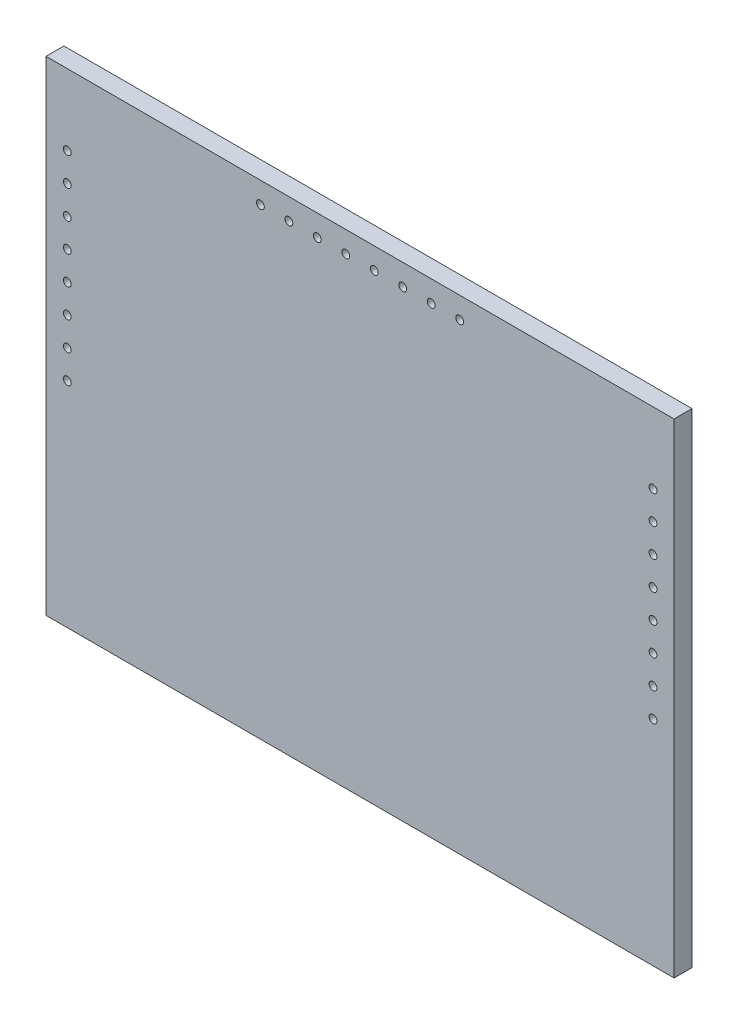
SolidWorks part; units mm, degrees
ref_plane "Plano frontal" through (0, 0, 0) normal (0, 0, 1) x (1, 0, 0)
ref_plane "Plano superior" through (0, 0, 0) normal (0, 1, 0) x (1, 0, 0)
ref_plane "Plano direito" through (0, 0, 0) normal (1, 0, 0) x (0, 0, -1)
sketch "Esboço1" plane through (0, 0, 0) normal (0, 0, 1) x (1, 0, 0)
  line L1 (-140.25, 108.115) -> (140.25, 108.115)
  line L2 (-140.25, 108.115) -> (-140.25, -108.115)
  line L3 (-140.25, -108.115) -> (140.25, -108.115)
  line L4 (140.25, 108.115) -> (140.25, -108.115)
  line L5 (-140.25, 108.115) -> (140.25, -108.115) construction
  line L6 (-140.25, -108.115) -> (140.25, 108.115) construction
  point P0 (0, 0)
  dimension "D1" = 280.5
  dimension "D2" = 216.23
extrude "Ressalto-extrusão1" add sketch "Esboço1" along normal blind 8
sketch "Esboço2" plane through (0, 0, 8) normal (0, 0, 1) x (1, 0, 0)
  line L2 (140.25, 108.115) -> (-140.25, 108.115) construction
  line L3 (140.25, -108.115) -> (140.25, 108.115) construction
  circle A0 centre (44.5, 98.615) radius 1.75
  dimension "D1" = 3.5
  dimension "D2" = 95.75
  dimension "D3" = 9.5
extrude "Corte-extrusão1" cut sketch "Esboço2" against normal blind 100
pattern_linear "Padrão linear1" count 8 spacing 12.7143 along (-1, 0, 0) of "Corte-extrusão1"
sketch "Esboço3" plane through (0, 0, 0) normal (0, 0, -1) x (-1, 0, 0)
  line L0 (140.25, 108.115) -> (140.25, -108.115) construction
  line L1 (-140.25, 108.115) -> (140.25, 108.115) construction
  circle A0 centre (130.75, 76.385) radius 1.75
  dimension "D1" = 3.5
  dimension "D2" = 9.5
  dimension "D3" = 31.73
extrude "Corte-extrusão2" cut sketch "Esboço3" against normal blind 10
pattern_linear "Padrão linear2" count 8 spacing 12.7143 along (0, -1, 0) count 2 spacing 261.6 along (1, 0, 0) of "Corte-extrusão2"
